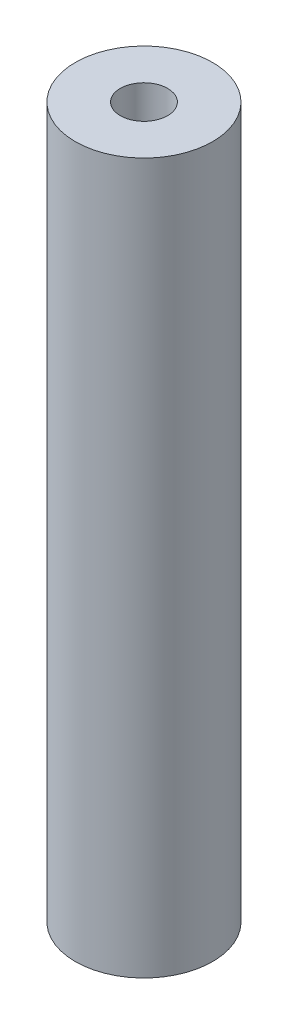
SolidWorks part; units mm, degrees
ref_plane "前视基准面" through (0, 0, 0) normal (0, 0, 1) x (1, 0, 0)
ref_plane "上视基准面" through (0, 0, 0) normal (0, 1, 0) x (1, 0, 0)
ref_plane "右视基准面" through (0, 0, 0) normal (1, 0, 0) x (0, 0, -1)
sketch "草图1" plane through (0, 0, 0) normal (0, 1, 0) x (1, 0, 0)
  circle A0 centre (-1.479, 0.6178) radius 2.9
  circle A1 centre (-1.479, 0.6178) radius 1
  dimension "D1" = 2
  dimension "D2" = 5.8
extrude "凸台-拉伸1" add sketch "草图1" along normal blind 30
